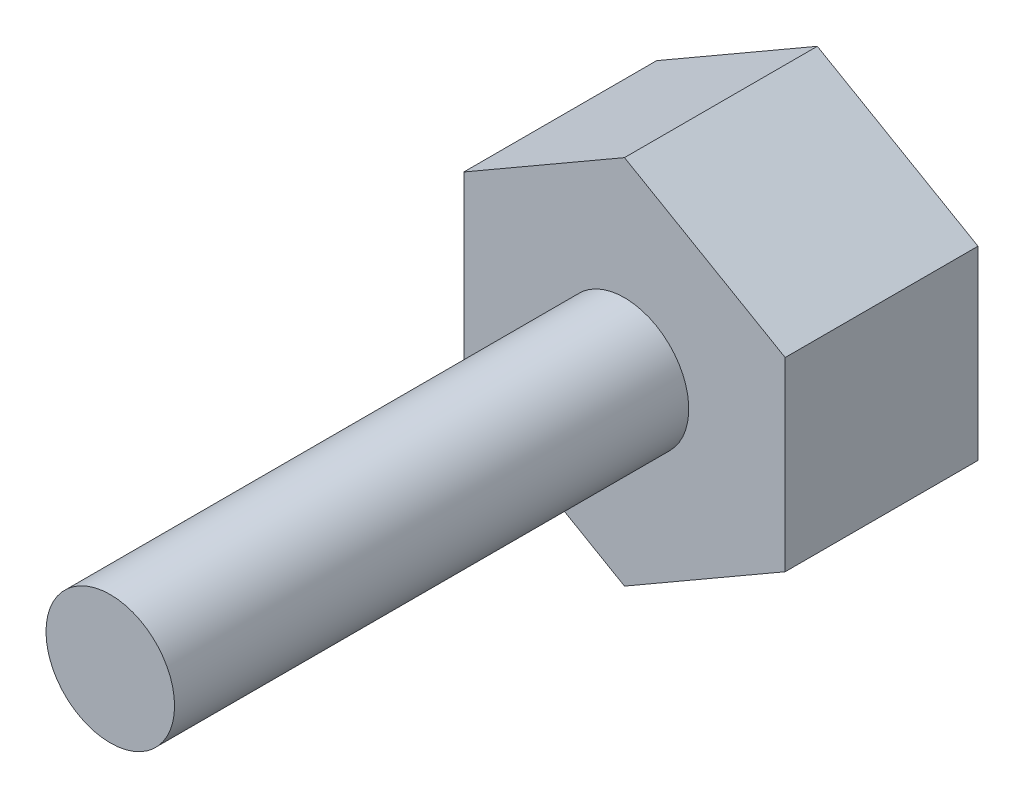
SolidWorks part; units mm, degrees
ref_plane "Front Plane" through (0, 0, 0) normal (0, 0, 1) x (1, 0, 0)
ref_plane "Top Plane" through (0, 0, 0) normal (0, 1, 0) x (1, 0, 0)
ref_plane "Right Plane" through (0, 0, 0) normal (1, 0, 0) x (0, 0, -1)
sketch "Sketch1" plane through (0, 0, 0) normal (0, 0, 1) x (1, 0, 0)
  circle A0 centre (-63.4948, 14.9787) radius 1
extrude "Boss-Extrude1" add sketch "Sketch1" along normal blind 8
sketch "Sketch2" plane through (0, 0, 0) normal (0, 0, -1) x (-1, 0, 0)
  line L1 (63.4948, 12.092) -> (65.9948, 13.5353)
  line L2 (65.9948, 13.5353) -> (65.9948, 16.4221)
  line L3 (65.9948, 16.4221) -> (63.4948, 17.8655)
  line L4 (63.4948, 17.8655) -> (60.9948, 16.4221)
  line L5 (60.9948, 16.4221) -> (60.9948, 13.5353)
  line L6 (60.9948, 13.5353) -> (63.4948, 12.092)
  circle A0 centre (63.4948, 14.9787) radius 2.5 construction
  dimension "D1" = 5
extrude "Boss-Extrude2" add sketch "Sketch2" along normal blind 3
